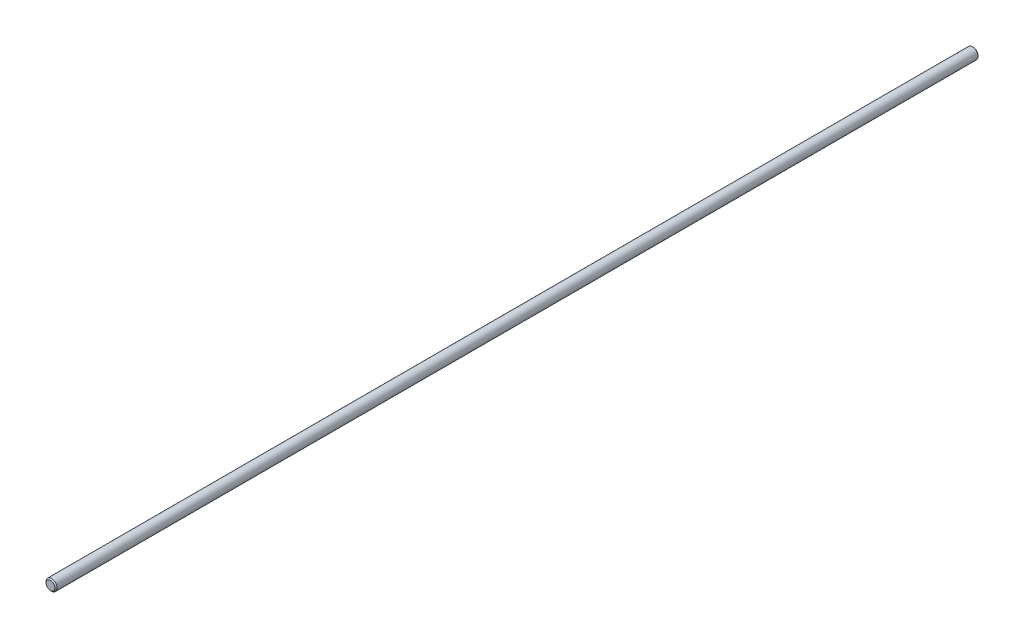
SolidWorks part; units mm, degrees
ref_plane "Plan de face" through (0, 0, 0) normal (0, 0, 1) x (1, 0, 0)
ref_plane "Plan de dessus" through (0, 0, 0) normal (0, 1, 0) x (1, 0, 0)
ref_plane "Plan de droite" through (0, 0, 0) normal (1, 0, 0) x (0, 0, -1)
sketch "Esquisse1" plane through (0, 0, 0) normal (0, 0, 1) x (1, 0, 0)
  circle A0 centre (0, 0) radius 3
  dimension "D1" = 6
extrude "Boss.-Extru.1" add sketch "Esquisse1" along normal blind 500
chamfer "Chanfrein1" distance 0.6 angle 45 2 edges at (3, 0, 500) (3, 0, 0)
